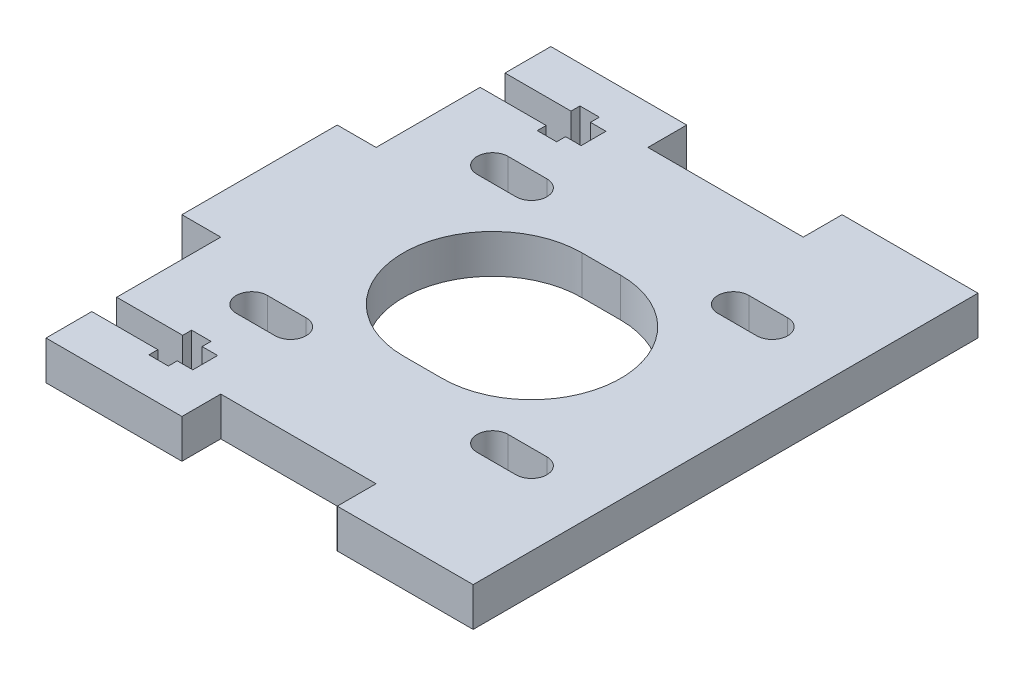
SolidWorks part; units mm, degrees
ref_plane "Plan de face" through (0, 0, 0) normal (0, 0, 1) x (1, 0, 0)
ref_plane "Plan de dessus" through (0, 0, 0) normal (0, 1, 0) x (1, 0, 0)
ref_plane "Plan de droite" through (0, 0, 0) normal (1, 0, 0) x (0, 0, -1)
sketch "Esquisse1" plane through (0, 0, 0) normal (0, 1, 0) x (1, 0, 0)
  line L1 (17.5, -5) -> (37.5, -5)
  line L3 (17.5, -60) -> (37.5, -60)
  line L5 (0, 0) -> (17.5, 0)
  line L6 (17.5, 0) -> (17.5, -5)
  line L7 (37.5, -5) -> (37.5, 0)
  line L8 (37.5, 0) -> (55, 0)
  line L10 (55, -32.5) -> (31.3794, -32.5) construction
  line L11 (55, 0) -> (55, -60)
  line L12 (0, 0) -> (0, -22.5)
  line L13 (0, -60) -> (0, -65)
  line L14 (0, -65) -> (17.5, -65)
  line L15 (17.5, -65) -> (17.5, -60)
  line L16 (55, -60) -> (55, -65)
  line L17 (55, -65) -> (37.5, -65)
  line L18 (37.5, -65) -> (37.5, -60)
  line L19 (27.5, -5) -> (27.5, -47.0906) construction
  line L20 (0, -22.5) -> (-5, -22.5)
  line L21 (-5, -22.5) -> (-5, -42.5)
  line L22 (-5, -42.5) -> (0, -42.5)
  line L23 (0, -42.5) -> (0, -60)
  dimension "D2" = 55
  dimension "D3" = 20
  dimension "D5" = 5
  dimension "D1" = 55
  dimension "D6" = 5
  dimension "D4" = 27.5
  dimension "D7" = 20
  dimension "D9" = 5
  dimension "D8" = 27.5
  dimension "D10" = 10
extrude "Boss.-Extru.1" add sketch "Esquisse1" along normal blind 5
sketch "Esquisse2" plane through (0, 5, 0) normal (0, 1, 0) x (1, 0, 0)
  line L0 (27.5, -5) -> (27.5, -60) construction
  line L3 (-5, -32.5) -> (47.7144, -32.5) construction
  line L4 (-5, -22.5) -> (-5, -42.5) construction
  line L5 (37.5, -5) -> (17.5, -5) construction
  line L6 (17.5, -60) -> (37.5, -60) construction
  line L7 (25, -32.5) -> (30, -32.5) construction
  line L8 (25, -21) -> (30, -21)
  line L9 (25, -44) -> (30, -44)
  arc A1 (25, -21) -> (25, -44) centre (25, -32.5) ccw
  arc A2 (30, -44) -> (30, -21) centre (30, -32.5) ccw
  point P12 (27.5, -32.5)
  point P13 (27.5, -32.5)
  dimension "D2" = 11.5
  dimension "D1" = 5
extrude "Enlèv. mat.-Extru.1" cut sketch "Esquisse2" against normal blind 5
sketch "Esquisse3" plane through (0, 5, 0) normal (0, 1, 0) x (1, 0, 0)
  line L0 (9.5, -17) -> (14.5, -17) construction
  line L1 (9.5, -15) -> (14.5, -15)
  line L2 (9.5, -19) -> (14.5, -19)
  line L3 (27.5, -5) -> (27.5, -60) construction
  line L4 (37.5, -5) -> (17.5, -5) construction
  line L5 (17.5, -60) -> (37.5, -60) construction
  line L6 (-5, -32.5) -> (55, -32.5) construction
  line L7 (-5, -22.5) -> (-5, -42.5) construction
  line L8 (55, -65) -> (55, 0) construction
  arc A0 (9.5, -15) -> (9.5, -19) centre (9.5, -17) ccw
  arc A1 (14.5, -19) -> (14.5, -15) centre (14.5, -17) ccw
  point P2 (12, -17)
  dimension "D1" = 15.5
  dimension "D2" = 4
  dimension "D3" = 15.5
  dimension "D4" = 5
extrude "Enlèv. mat.-Extru.2" cut sketch "Esquisse3" against normal blind 5
ref_plane "Plan1" through (27.5, 0, 0) normal (-1, 0, 0) x (0, 0, 1)
ref_plane "Plan2" through (0, 0, 32.5) normal (0, 0, 1) x (1, 0, 0)
mirror "Symétrie1" about plane through (0, 0, 32.5) normal (0, 0, 1) of "Enlèv. mat.-Extru.2"
mirror "Symétrie2" about plane through (27.5, 0, 0) normal (-1, 0, 0) of "Symétrie1", "Enlèv. mat.-Extru.2"
sketch "Esquisse4" plane through (0, 5, 0) normal (0, 1, 0) x (1, 0, 0)
  line L1 (13, -5.9) -> (11, -5.9)
  line L2 (13, -5.9) -> (13, -9.1)
  line L3 (13, -9.1) -> (11, -9.1)
  line L4 (0, -5.9) -> (0, -9.1)
  line L5 (-5, -32.5) -> (9.8768, -32.5) construction
  line L6 (-5, -22.5) -> (-5, -42.5) construction
  line L7 (13, -7.5) -> (0, -7.5) construction
  line L8 (11, -5.9) -> (11, -4.75)
  line L9 (11, -4.75) -> (8.5, -4.75)
  line L10 (8.5, -4.75) -> (8.5, -5.9)
  line L11 (8.5, -5.9) -> (0, -5.9)
  line L12 (11, -9.1) -> (11, -10.25)
  line L13 (11, -10.25) -> (8.5, -10.25)
  line L14 (8.5, -10.25) -> (8.5, -9.1)
  line L15 (8.5, -9.1) -> (0, -9.1)
  line L16 (0, 0) -> (0, -22.5) construction
  point P17 (9.75, -10.25)
  point P19 (11, -9.675)
  dimension "D1" = 25
  dimension "D2" = 3.2
  dimension "D3" = 13
  dimension "D4" = 5.5
  dimension "D5" = 2.75
  dimension "D6" = 2.5
  dimension "D7" = 2
extrude "Enlèv. mat.-Extru.3" cut sketch "Esquisse4" against normal blind 10
mirror "Symétrie3" about plane through (0, 0, 32.5) normal (0, 0, 1) of "Enlèv. mat.-Extru.3"
equation "\"D6@Esquisse1\"=\"D5@Esquisse1\""
equation "\"D4@Esquisse1\"=\"D2@Esquisse1\"/2"
equation "\"D9@Esquisse1\"=\"D5@Esquisse1\""
equation "\"D8@Esquisse1\"=\"D1@Esquisse1\"/2"
equation "\"D10@Esquisse1\"=\"D7@Esquisse1\"/2"
equation "\"D3@Esquisse3\"=31/2"
equation "\"D1@Esquisse3\"=31/2"
equation "\"D5@Esquisse4\"=\"D4@Esquisse4\"/2"
